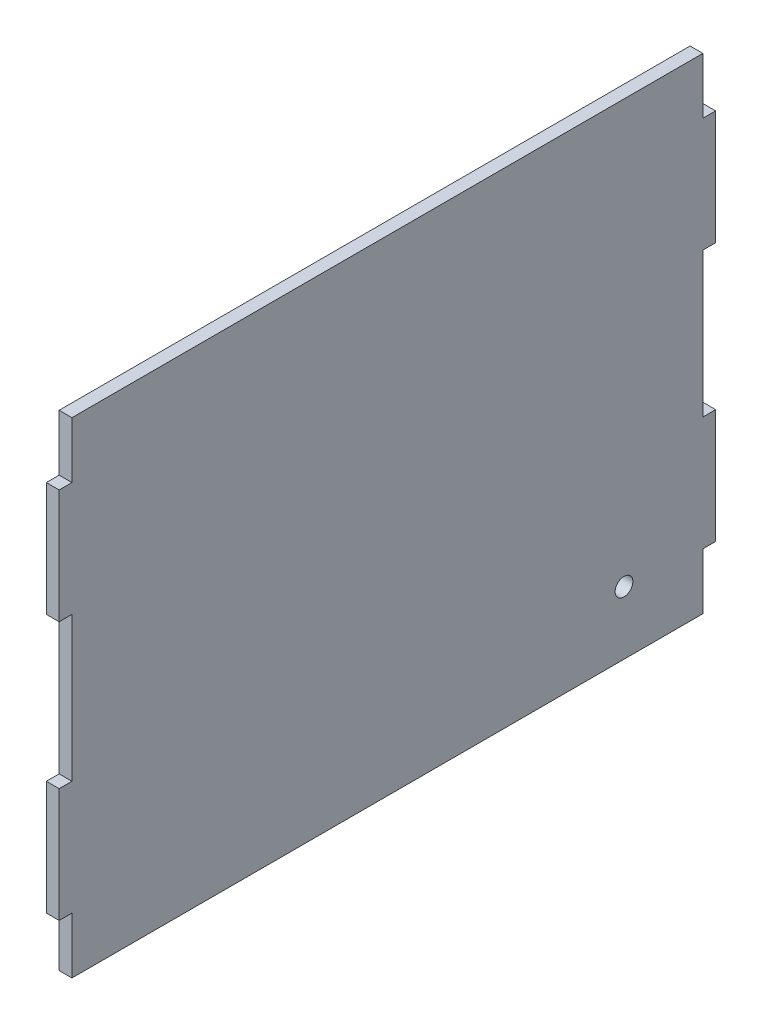
SolidWorks part; units mm, degrees
ref_plane "Front Plane" through (0, 0, 0) normal (0, 0, 1) x (1, 0, 0)
ref_plane "Top Plane" through (0, 0, 0) normal (0, 1, 0) x (1, 0, 0)
ref_plane "Right Plane" through (0, 0, 0) normal (1, 0, 0) x (0, 0, -1)
sketch "Sketch1" plane through (0, 0, 0) normal (1, 0, 0) x (0, 0, -1)
  line L0 (-140.35, 82.95) -> (-140.35, 107.95)
  line L7 (-146.05, 82.95) -> (-146.05, 32.15)
  line L9 (-146.05, -82.95) -> (-140.35, -82.95)
  line L11 (-140.35, -32.15) -> (-146.05, -32.15)
  line L13 (-146.05, 82.95) -> (-140.35, 82.95)
  line L16 (-140.35, 32.15) -> (-146.05, 32.15)
  line L44 (-140.35, 32.15) -> (-140.35, -32.15)
  line L45 (-146.05, -32.15) -> (-146.05, -82.95)
  line L46 (-140.35, -82.95) -> (-140.35, -107.95)
  line L47 (0, 0) -> (0, 107.95) construction
  line L57 (0, 0) -> (140.35, 0) construction
  line L60 (-140.35, 107.95) -> (140.35, 107.95)
  line L62 (146.05, -32.15) -> (146.05, -82.95)
  line L63 (140.35, 32.15) -> (140.35, -32.15)
  line L64 (140.35, 32.15) -> (146.05, 32.15)
  line L65 (146.05, 82.95) -> (140.35, 82.95)
  line L66 (140.35, -32.15) -> (146.05, -32.15)
  line L67 (146.05, -82.95) -> (140.35, -82.95)
  line L68 (146.05, 82.95) -> (146.05, 32.15)
  line L69 (140.35, 82.95) -> (140.35, 107.95)
  line L70 (140.35, -82.95) -> (140.35, -107.95)
  line L71 (-140.35, -107.95) -> (140.35, -107.95)
  point P0 (0, 0)
  point P18 (-146.05, 0)
  point P24 (146.05, 0)
  dimension "D4" = 5.7
extrude "Boss-Extrude1" add sketch "Sketch1" along normal blind 5.7
sketch "Sketch2" plane through (5.7, 0, 0) normal (1, 0, 0) x (0, 0, -1)
  line L0 (70.175, 0) -> (140.35, 0) construction
  line L2 (70.175, 0) -> (70.175, -107.95) construction
  line L3 (-140.35, -107.95) -> (140.35, -107.95) construction
  line L4 (140.35, -32.15) -> (140.35, 32.15) construction
  line L5 (105.2625, 0) -> (105.2625, -79.9707) construction
  circle A0 centre (105.2625, -79.9707) radius 3.95
  point P2 (105.2625, -79.9707)
  point P11 (0, 0)
  dimension "D1" = 7.9
  dimension "D2" = 70.175
extrude "Cut-Extrude1" cut sketch "Sketch2" against normal blind 10
